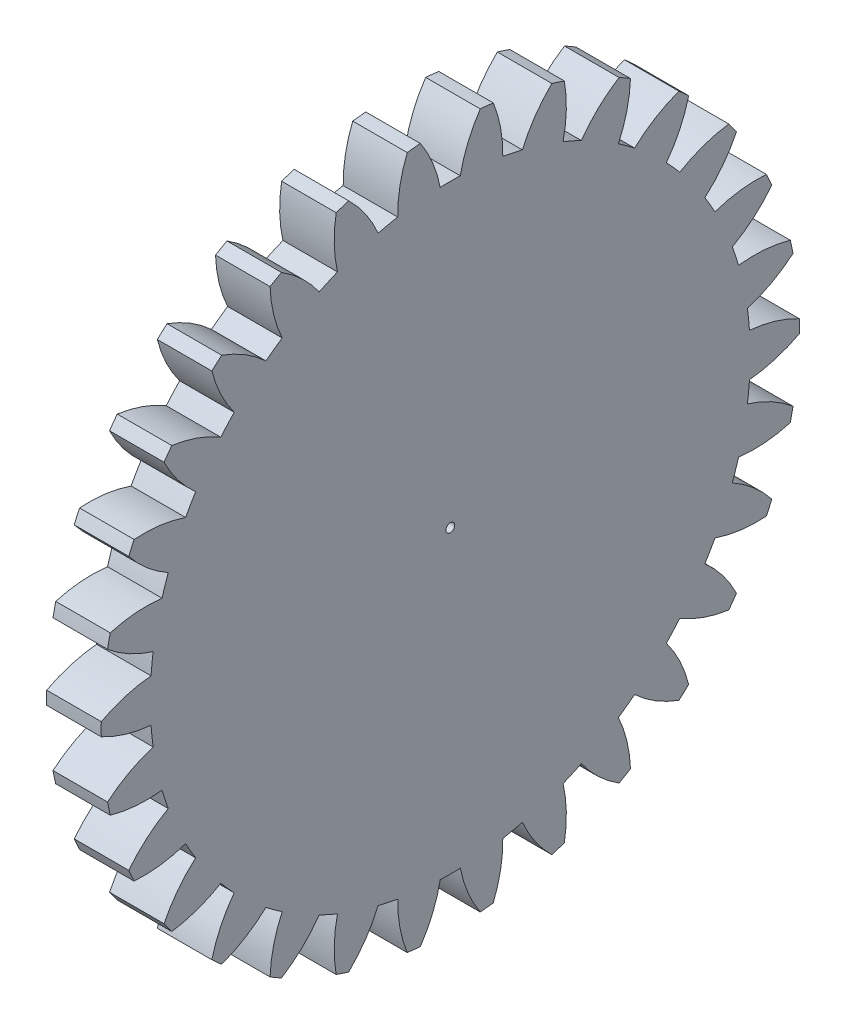
SolidWorks part; units mm, degrees
ref_plane "Plane1" through (0, 0, 0) normal (0, 0, 1) x (1, 0, 0)
ref_plane "Plane2" through (0, 0, 0) normal (0, 1, 0) x (1, 0, 0)
ref_plane "Plane3" through (0, 0, 0) normal (1, 0, 0) x (0, 0, -1)
other "Configuration Table"
sketch "HoldingSke" plane through (0, 0, 0) normal (0, 1, 0) x (1, 0, 0)
  line L0 (0, 0) -> (0.433, -0.25)
  line L1 (-15, 0) -> (100, 0) construction
  line L2 (0, 0) -> (-2.1039, 2.3779)
  line L3 (0, 0) -> (-11.863, 4.5341)
  line L4 (0, 0) -> (7.479, 4.318)
  line L5 (0, 0) -> (-46.8476, -17.4728)
  line L6 (0, 0) -> (-4.1448, -2.7965)
  line L7 (-2.1039, 2.3779) -> (8.6586, 51.2059)
  line L8 (-76.2, 54.61) -> (-76.1, 54.61)
  line L9 (-71.009, 38.7566) -> (-53.1078, 45.2721)
  line L10 (-76.2, 71.12) -> (104.1128, 71.12)
  line L11 (0, 0) -> (-5, 0)
  line L12 (-76.2, 101.6) -> (-76.133, 101.6)
  line L13 (24.9733, 27.94) -> (52.9518, 28.4284)
  line L14 (24.9733, 27.94) -> (24.9743, 27.94)
  line L15 (24.9733, 27.94) -> (100.4006, 29.5858)
  line L16 (-63.627, -2) -> (-12.827, -2)
  circle A0 centre (0, 0) radius 0.4
  circle A1 centre (0, 0) radius 27.499
  circle A2 centre (0, 0) radius 37.5
  circle A3 centre (0, 0) radius 0.4
  dimension "Hub_dia" = 75
  dimension "Overall_len" = 50
  dimension "OAL" = 50.0001
  dimension "Ap" = 20
  dimension "H" = 19.05
  dimension "Pitch_radius" = 180.3128
  dimension "Addendum_fac" = 1
  dimension "Dedendum_fac" = 1.25
  dimension "Clearance_fac" = 0.25
  dimension "Dedendum_add" = 0.001
sketch "BasProSke" plane through (0, 0, 0) normal (0, 1, 0) x (1, 0, 0)
  line L0 (-10, 0) -> (60, 0) construction
  line L1 (0, 0) -> (0, 32)
  line L2 (0, 0) -> (5, 0)
  line L3 (5, 0) -> (5, 32)
  line L4 (5, 32) -> (0, 32)
revolve "Base-Revolve" add sketch "BasProSke" angle 360 about L0
sketch "TooCutSke" plane through (0, 0, 0) normal (1, 0, 0) x (0, 0, -1)
  line L1 (0, 0) -> (0, 107) construction
  line L2 (0, 0) -> (-1.6873, 29.9525) construction
  line L3 (0, 0) -> (-6.2643, 59.6013) construction
  line L4 (-1.6873, 29.9525) -> (-3.1322, 29.8007) construction
  arc A0 (0.9186, 27.4837) -> (-0.9186, 27.4837) centre (0, 0) ccw
  arc A1 (2.7618, 31.9061) -> (-2.7618, 31.9061) centre (0, 0) ccw
  circle A2 centre (0, 0) radius 30 construction
  circle A3 centre (0, 0) radius 28.1908 construction
  arc A4 (-0.9186, 27.4837) -> (-2.7618, 31.9061) centre (-12.6936, 25.1712) ccw
  arc A5 (2.7618, 31.9061) -> (0.9186, 27.4837) centre (12.6936, 25.1712) ccw
extrude "ToothCut" cut sketch "TooCutSke" along normal through all
fillet "Breaks" [suppressed] radius 0.04
fillet "RootFillets" [suppressed] radius 0.501
pattern_circular "TeethCuts" count 30 every 12 about axis through (-10, 0, 0) along (1, 0, 0) of "ToothCut", "RootFillets", "Breaks"
sketch "HubNeaOneSke" plane through (0, 0, 0) normal (-1, 0, 0) x (0, 0, 1)
  circle A0 centre (0, 0) radius 27.499
extrude "HubNearOne" [suppressed] add sketch "HubNeaOneSke" along normal blind 45.0001
sketch "HubNeaBotSke" plane through (0, 0, 0) normal (-1, 0, 0) x (0, 0, 1)
  circle A0 centre (0, 0) radius 27.499
extrude "HubNearBoth" [suppressed] add sketch "HubNeaBotSke" along normal blind 22.5
ref_plane "FarPln" through (5, 0, 0) normal (1, 0, 0) x (0, 0, -1)
sketch "HubFarSke" plane through (5, 0, 0) normal (1, 0, 0) x (0, 0, -1)
  circle A0 centre (0, 0) radius 27.499
extrude "HubFar" [suppressed] add sketch "HubFarSke" along normal blind 22.5
sketch "BorSke" plane through (0, 0, 0) normal (1, 0, 0) x (0, 0, -1)
  circle A0 centre (0, 0) radius 0.4
extrude "Bore" cut sketch "BorSke" along normal mid plane 100.0001
sketch "KeySke" plane through (0, 0, 0) normal (1, 0, 0) x (0, 0, -1)
  line L0 (-0.05, 0) -> (-0.05, 0.5)
  line L1 (-0.05, 0.5) -> (0.05, 0.5)
  line L2 (0.05, 0.5) -> (0.05, 0)
  line L3 (0, 0) -> (0, 34) construction
  line L4 (-0.05, 0) -> (0.05, 0)
extrude "Keyway" [suppressed] cut sketch "KeySke" along normal mid plane 100.0001
pattern_circular "Keyway2" [suppressed] count 2 every 90 about axis through (-10, 0, 0) along (1, 0, 0)
equation "' \"Module@HoldingSke\" = 6.35"
equation "' \"Num_teeth@HoldingSke\" = 12"
equation "' \"Ap@HoldingSke\" =  20"
equation "' \"Ap@HoldingSke\" = 20"
equation "' \"Width@HoldingSke\" = 0.5 * 25.4"
equation "' \"Hub_dia@HoldingSke\"= 1 * 25.4"
equation "' \"Hub_dia@HoldingSke\" = 1 * 25.4"
equation "' \"Overall_len@HoldingSke\" = 1.0 * 25.4"
equation "' \"Bore@HoldingSke\" = 0.75 * 25.4"
equation "' \"T_dim@HoldingSke\" = 0.1 * 25.4"
equation "' \"Width@KeySke\" = 0.25 * 25.4"
equation "' \"Show_teeth@HoldingSke\" = 13"
equation "' \"Backlash@HoldingSke\" = 0.009 * 25.4"
equation "' \"Addendum_fac@HoldingSke\" = 1.0"
equation "' \"Dedendum_fac@HoldingSke\" = 1.25"
equation "' \"Dedendum_add@HoldingSke\" = 0.00005 * 25.4"
equation "' \"Clearance_fac@HoldingSke\" = 0.25"
equation "\"Pitch@HoldingSke\" = 1 / \"Module@HoldingSke\""
equation "\"Overcut_dia@TooCutSke\" = (\"Num_teeth@HoldingSke\" + 2 * \"Addendum_fac@HoldingSke\") / \"Pitch@HoldingSke\" + 0.002 * 25.4"
equation "\"Pitch_dia@TooCutSke\" = \"Num_teeth@HoldingSke\" / \"Pitch@HoldingSke\""
equation "\"Base_dia@TooCutSke\" = \"Num_teeth@HoldingSke\" / \"Pitch@HoldingSke\" * cos((\"Ap@HoldingSke\"  * 3.14159265 / 180))"
equation "\"Root_dia@TooCutSke\" = (\"Num_teeth@HoldingSke\" + 2) / \"Pitch@HoldingSke\" - 2 * (\"Addendum_fac@HoldingSke\" + \"Dedendum_fac@HoldingSke\") / \"Pitch@HoldingSke\" - \"Dedendum_add@HoldingSke\" * 2"
equation "\"Half_ang@TooCutSke\" = 180 / \"Num_teeth@HoldingSke\""
equation "\"Half_CT@TooCutSke\" = \"Num_teeth@HoldingSke\" / \"Pitch@HoldingSke\" * sin((3.14159265 / 2 / \"Num_teeth@HoldingSke\")) / 2 - 7 * \"Backlash@HoldingSke\" / 4"
equation "\"Flank_rad@TooCutSke\" = \"Num_teeth@HoldingSke\" / \"Pitch@HoldingSke\" / 5"
equation "\"Radius@RootFillets\" = \"Clearance_fac@HoldingSke\" / \"Pitch@HoldingSke\" + \"Dedendum_add@HoldingSke\""
equation "\"Break_rad@Breaks\" = 0.02 / \"Pitch@HoldingSke\""
equation "\"Thickness@HoldingSke\" = \"Width@HoldingSke\""
equation "\"OAL@HoldingSke\" = \"Thickness@HoldingSke\""
equation "\"MHD@HoldingSke\" = (\"Num_teeth@HoldingSke\" + 2) / \"Pitch@HoldingSke\" - 2 * (\"Addendum_fac@HoldingSke\" + \"Dedendum_fac@HoldingSke\")  / \"Pitch@HoldingSke\" - \"Dedendum_add@HoldingSke\" * 2"
equation "\"MBD@HoldingSke\" = (\"Num_teeth@HoldingSke\" + 2) / \"Pitch@HoldingSke\" - 2 * (\"Addendum_fac@HoldingSke\" + \"Dedendum_fac@HoldingSke\")  / \"Pitch@HoldingSke\" - \"Dedendum_add@HoldingSke\" * 2 - 0.002 * 25.4"
equation "\"MHD@HoldingSke\" = ((sgn( \"MHD@HoldingSke\" - \"Hub_dia@HoldingSke\" )-1)*( \"MHD@HoldingSke\" - \"Hub_dia@HoldingSke\" ))/-2+ \"Hub_dia@HoldingSke\""
equation "\"MBD@HoldingSke\" = ((sgn( \"MBD@HoldingSke\" - \"Bore@HoldingSke\" )-1)*( \"MBD@HoldingSke\" - \"Bore@HoldingSke\" ))/-2+ \"Bore@HoldingSke\""
equation "\"OAL@HoldingSke\" = ((sgn( \"OAL@HoldingSke\" - \"Overall_len@HoldingSke\" )+1)*( \"OAL@HoldingSke\" - \"Overall_len@HoldingSke\" ))/2 + \"Overall_len@HoldingSke\" + 0.000002 * 25.4"
equation "\"Num_teeth@TeethCuts\" = int( \"Show_teeth@HoldingSke\" ) + 1"
equation "\"Num_teeth@TeethCuts\" = ((sgn( \"Num_teeth@TeethCuts\" - \"Num_teeth@HoldingSke\" )-1)*( \"Num_teeth@TeethCuts\" - \"Num_teeth@HoldingSke\" ))/-2+ \"Num_teeth@HoldingSke\""
equation "\"Num_teeth@TeethCuts\" = ((sgn( \"Num_teeth@TeethCuts\" - 2.0)+1)*( \"Num_teeth@TeethCuts\" - 2.0))/2 +2.0"
equation "\"Angle@TeethCuts\" = 360.0 / \"Num_teeth@HoldingSke\""
equation "\"Diameter@BasProSke\" = (\"Num_teeth@HoldingSke\" + 2 * \"Addendum_fac@HoldingSke\") / \"Pitch@HoldingSke\""
equation "\"Thickness@BasProSke\"  = \"Thickness@HoldingSke\""
equation "' \"Fillet_rad@BasProSke\" =  \"Thickness@HoldingSke\" * 0.05"
equation "' \"Fillet_rad@BasProSke\" = \"Thickness@HoldingSke\" * 0.05"
equation "\"MHD@HoldingSke\" = ((sgn( \"MHD@HoldingSke\" - \"Root_dia@TooCutSke\" )-1)*( \"MHD@HoldingSke\" - \"Root_dia@TooCutSke\" ))/-2+ \"Root_dia@TooCutSke\""
equation "\"Diameter@HubNeaOneSke\" = \"MHD@HoldingSke\""
equation "\"Length@HubNearOne\" = \"OAL@HoldingSke\" - \"Thickness@BasProSke\""
equation "\"Diameter@HubNeaBotSke\" = \"MHD@HoldingSke\""
equation "\"Length@HubNearBoth\" = ( \"OAL@HoldingSke\" - \"Thickness@BasProSke\" ) / 2.0"
equation "\"Thickness@FarPln\" = \"Thickness@BasProSke\""
equation "\"Diameter@HubFarSke\" = \"MHD@HoldingSke\""
equation "\"Length@HubFar\" = ( \"OAL@HoldingSke\" - \"Thickness@BasProSke\" ) / 2.0"
equation "\"Diameter@BorSke\" = \"MBD@HoldingSke\""
equation "\"D1@Bore\" = \"OAL@HoldingSke\" * 2.0"
equation "\"D1@Keyway\" = \"OAL@HoldingSke\" * 2.0"
equation "\"Offset@KeySke\" = \"T_dim@HoldingSke\" + \"MBD@HoldingSke\" / 2.0"
